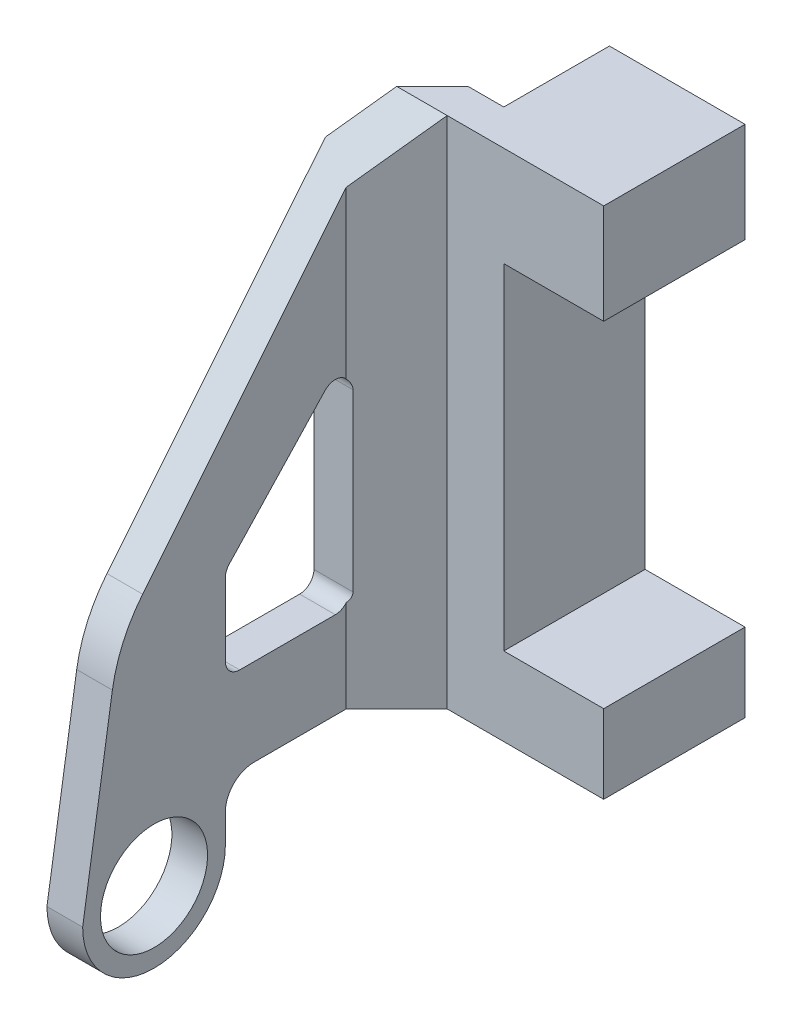
SolidWorks part; units mm, degrees
ref_plane "Płaszczyzna przednia" through (0, 0, 0) normal (0, 0, 1) x (1, 0, 0)
ref_plane "Płaszczyzna górna" through (0, 0, 0) normal (0, 1, 0) x (1, 0, 0)
ref_plane "Płaszczyzna prawa" through (0, 0, 0) normal (1, 0, 0) x (0, 0, -1)
sketch "Szkic1" plane through (0, 0, 0) normal (0, 0, 1) x (1, 0, 0)
  line L0 (0, 0) -> (0, 36)
  line L1 (0, 36) -> (-9.5, 36)
  line L2 (-9.5, 36) -> (-9.5, 0)
  line L3 (-9.5, 0) -> (0, 0)
  dimension "D1" = 9.5
  dimension "D2" = 36
extrude "Dodanie-wyciągnięcie1" add sketch "Szkic1" along normal blind 9.9
sketch "Szkic2" plane through (0, 0, 9.9) normal (0, 0, 1) x (1, 0, 0)
  line L0 (0, 29) -> (-7, 29)
  line L1 (0, 0) -> (0, 36) construction
  line L2 (-7, 29) -> (-7, 5.5)
  line L3 (-7, 5.5) -> (0, 5.5)
  line L4 (0, 5.5) -> (0, 29)
  line L5 (0, 36) -> (-9.5, 36) construction
  dimension "D1" = 7
  dimension "D2" = 23.5
  dimension "D3" = 7
extrude "Wytnij-wyciągnięcie1" cut sketch "Szkic2" against normal blind 9.9
sketch "Szkic3" plane through (-9.5, 0, 0) normal (-1, 0, 0) x (0, 0, 1)
  line L0 (7.4, 36) -> (9.9, 36) construction
  line L1 (7.4, 0) -> (7.4, 36) construction
  line L2 (9.9, 36) -> (12.4, 32.9231) construction
  line L3 (29.4, 12) -> (12.4, 32.9231) construction
  line L4 (31.9, -4) -> (29.4, 12) construction
  line L5 (21.9, 0) -> (21.9, -4) construction
  line L6 (12.4, 0) -> (21.9, 0) construction
  line L7 (7.4, 0) -> (12.4, 0) construction
  line L8 (7.4, 36) -> (9.9, 36)
  line L9 (7.4, 0) -> (7.4, 36)
  line L10 (9.9, 36) -> (12.4, 32.9231)
  line L11 (29.4, 12) -> (12.4, 32.9231)
  line L12 (31.9, -4) -> (29.4, 12)
  line L13 (21.9, 0) -> (21.9, -4)
  line L14 (12.4, 0) -> (21.9, 0)
  line L15 (7.4, 0) -> (12.4, 0)
  circle A0 centre (26.9, -4) radius 2.5 construction
  arc A1 (21.9, -4) -> (31.9, -4) centre (26.9, -4) ccw construction
  circle A2 centre (26.9, -4) radius 2.5
  arc A3 (21.9, -4) -> (31.9, -4) centre (26.9, -4) ccw
extrude "Dodanie-wyciągnięcie2" add sketch "Szkic3" along normal blind 7.5
sketch "Szkic4" plane through (0, 36, 0) normal (0, 1, 0) x (1, 0, 0)
  line L0 (-12, -7.4) -> (-22.2511, -17.6511)
  line L1 (-17, -7.4) -> (-9.5, -7.4) construction
  line L2 (-9.5, -7.4) -> (-9.5, 0) construction
  line L3 (-12, -7.4) -> (-26.526, -7.4)
  line L4 (-26.526, -7.4) -> (-22.2511, -17.6511)
  line L5 (-10.9645, -9.9) -> (-14.5, -13.4355)
  line L6 (-17, -9.9) -> (-9.5, -9.9) construction
  line L7 (-14.5, -13.4355) -> (-14.5, -34.971)
  line L8 (-14.5, -34.971) -> (-2.8566, -34.971)
  line L9 (-2.8566, -34.971) -> (-4.3843, -9.9)
  line L10 (0, -9.9) -> (-9.5, -9.9) construction
  line L11 (-4.3843, -9.9) -> (-10.9645, -9.9)
  line L12 (-17, -29.4) -> (-17, -9.9) construction
  dimension "D1" = 45
  dimension "D2" = 2.5
  dimension "D3" = 2.5
  dimension "D4" = 2.5
extrude "Wytnij-wyciągnięcie2" cut sketch "Szkic4" against normal blind 137.5
sketch "Szkic5" plane through (-17, 0, 0) normal (-1, 0, 0) x (0, 0, 1)
  line L0 (21.9, 12.2052) -> (21.9, 7.1) construction
  line L1 (21.9, 12.2052) -> (21.9, 7.1)
  line L2 (20.9, 6.1) -> (14.2, 6.1) construction
  line L3 (13.2, 7.1) -> (13.2, 19.3672) construction
  line L4 (14.9303, 20.0504) -> (21.6303, 12.8883) construction
  line L5 (12.4, 32.9231) -> (12.4, 0)
  line L6 (12.4, 0) -> (21.9, 0)
  line L7 (21.9, 0) -> (21.9, -4)
  line L8 (31.9, -4) -> (29.4, 12)
  line L9 (29.4, 12) -> (12.4, 32.9231)
  line L10 (12.4, 32.9231) -> (12.4, 0)
  line L11 (12.4, 0) -> (21.9, 0)
  line L12 (21.9, 0) -> (21.9, -4)
  line L13 (31.9, -4) -> (29.4, 12)
  line L14 (29.4, 12) -> (12.4, 32.9231)
  line L15 (20.9, 6.1) -> (14.2, 6.1)
  line L16 (13.2, 7.1) -> (13.2, 19.3672)
  line L17 (14.9303, 20.0504) -> (21.6303, 12.8883)
  arc A0 (21.9, 12.2052) -> (21.6303, 12.8883) centre (20.9, 12.2052) ccw construction
  arc A1 (21.9, -4) -> (31.9, -4) centre (26.9, -4) ccw
  arc A2 (21.9, -4) -> (31.9, -4) centre (26.9, -4) ccw
  arc A3 (21.9, 12.2052) -> (21.6303, 12.8883) centre (20.9, 12.2052) ccw
  arc A4 (20.9, 6.1) -> (21.9, 7.1) centre (20.9, 7.1) ccw construction
  arc A5 (13.2, 7.1) -> (14.2, 6.1) centre (14.2, 7.1) ccw construction
  arc A6 (14.9303, 20.0504) -> (13.2, 19.3672) centre (14.2, 19.3672) ccw construction
  arc A7 (20.9, 6.1) -> (21.9, 7.1) centre (20.9, 7.1) ccw
  arc A8 (13.2, 7.1) -> (14.2, 6.1) centre (14.2, 7.1) ccw
  arc A9 (14.9303, 20.0504) -> (13.2, 19.3672) centre (14.2, 19.3672) ccw
  dimension "D1" = 0
extrude "Wytnij-wyciągnięcie3" cut sketch "Szkic5" against normal blind 137.5 contours L17 A9 L16 A8 L15 A7 L1 A3
fillet "Zaokrąglenie1" radius 10 1 edges at (-15.75, 12, 29.4)
fillet "Zaokrąglenie2" radius 2 1 edges at (-15.75, 0, 21.9)
sketch "Szkic6" plane through (-17, 0, 0) normal (-1, 0, 0) x (0, 0, 1)
  circle A0 centre (26.9, -4) radius 3.75
  dimension "D1" = 7.5
extrude "Wytnij-wyciągnięcie4" cut sketch "Szkic6" against normal blind 10
